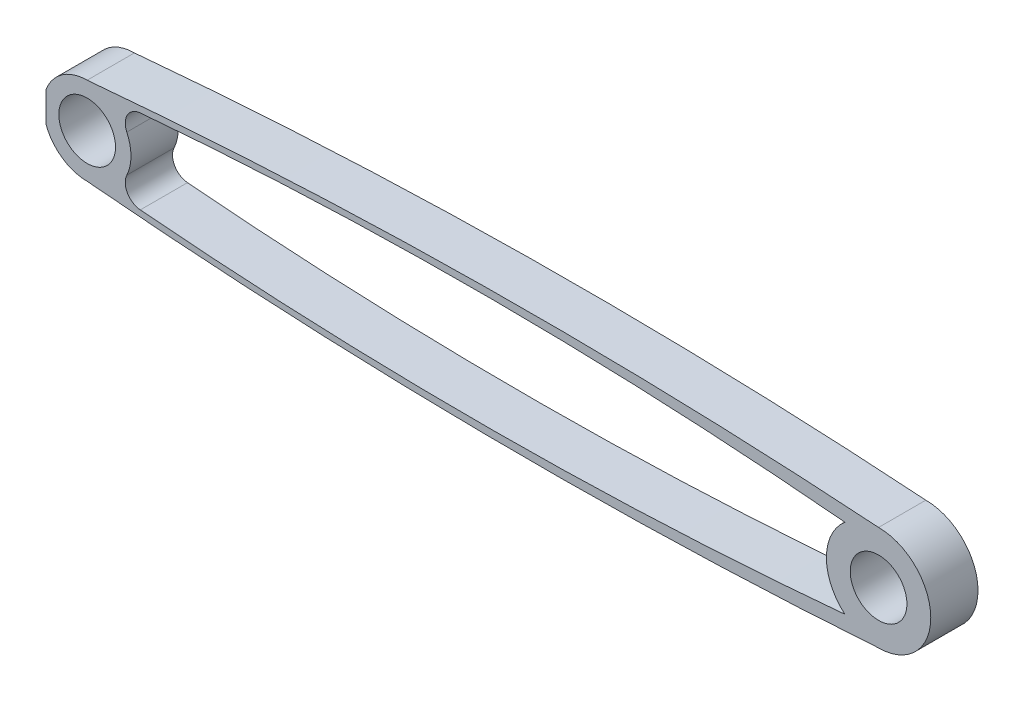
SolidWorks part; units mm, degrees
material "ABS"
ref_plane "Płaszczyzna przednia" through (0, 0, 0) normal (0, 0, 1) x (1, 0, 0)
ref_plane "Płaszczyzna górna" through (0, 0, 0) normal (0, 1, 0) x (1, 0, 0)
ref_plane "Płaszczyzna prawa" through (0, 0, 0) normal (1, 0, 0) x (0, 0, -1)
sketch "Szkic1" plane through (0, 0, 0) normal (0, 0, 1) x (1, 0, 0)
  line L0 (-3, 0) -> (83.7624, 0) construction
  line L1 (40.3812, 0) -> (40.3812, 21.7565) construction
  circle A0 centre (0, 0) radius 3
  circle A1 centre (83.7624, 0) radius 3
  circle A2 centre (83.7624, 0) radius 5.5226
  circle A3 centre (0, 0) radius 4.6352
  arc A4 (80.1994, 4.2195) -> (2.1049, 4.1297) centre (41.6354, -415.9215) ccw
  arc A5 (83.7624, -5.5226) -> (0, -4.6352) centre (47.425, 518.1828) cw
  arc A6 (83.7624, 5.5226) -> (0, 4.6352) centre (47.425, -518.1828) ccw
  arc A7 (80.1994, -4.2195) -> (2.1049, -4.1297) centre (41.6354, 415.9215) cw
  arc A9 (4.1943, 1.973) -> (5.6193, 4.4456) centre (5.7677, 2.7132) cw
  arc A10 (4.1943, -1.973) -> (5.6193, -4.4456) centre (5.7677, -2.7132) ccw
  point P7 (80.1994, -4.2195)
  point P15 (2.2014, -4.3191)
  point P28 (6.0446, -3.8337)
  point P29 (78.2402, 0)
  point P30 (0, 0)
  dimension "D1" = 83.7624
  dimension "D2" = 6
  dimension "D3" = 5.5226
  dimension "D4" = 4.6352
extrude "Dodanie-wyciągnięcie1" add sketch "Szkic1" along normal blind 5 contours A2 A1 | A3 A0 | A10 A3 A7 | A2 A7 A3 A5 | A3 A9 A4 | A2 A6 A3 A4
sketch "Szkic2" plane through (0, 0, 0) normal (0, 0, 1) x (1, 0, 0)
  line L0 (196.2931, 0) -> (-6.6873, 0) construction
  line L1 (192.8293, 4.1341) -> (192.8293, -3.3715)
  line L2 (-4.3568, -2.5646) -> (-4.3568, 2.4871)
  line L4 (-4.3568, 2.4871) -> (-5.0086, 2.4871)
  line L5 (-4.3568, 2.4871) -> (-4.3568, -2.5646)
  line L6 (-4.3568, -2.5646) -> (-5.0086, -2.5646)
  line L7 (-5.0086, 2.4871) -> (-5.0086, -2.5646)
  line L8 (192.8293, -3.3715) -> (194.4479, -3.3715)
  line L9 (192.8293, -3.3715) -> (192.8293, 4.1341)
  line L10 (192.8293, 4.1341) -> (194.4479, 4.1341)
  line L11 (194.4479, -3.3715) -> (194.4479, 4.1341)
extrude "Wytnij-wyciągnięcie3" cut sketch "Szkic2" along normal through all contours L0 L11 L10 L1 | L11 L0 L9 L8 | L0 L5 L4 L7 | L2 L0 L7 L6
